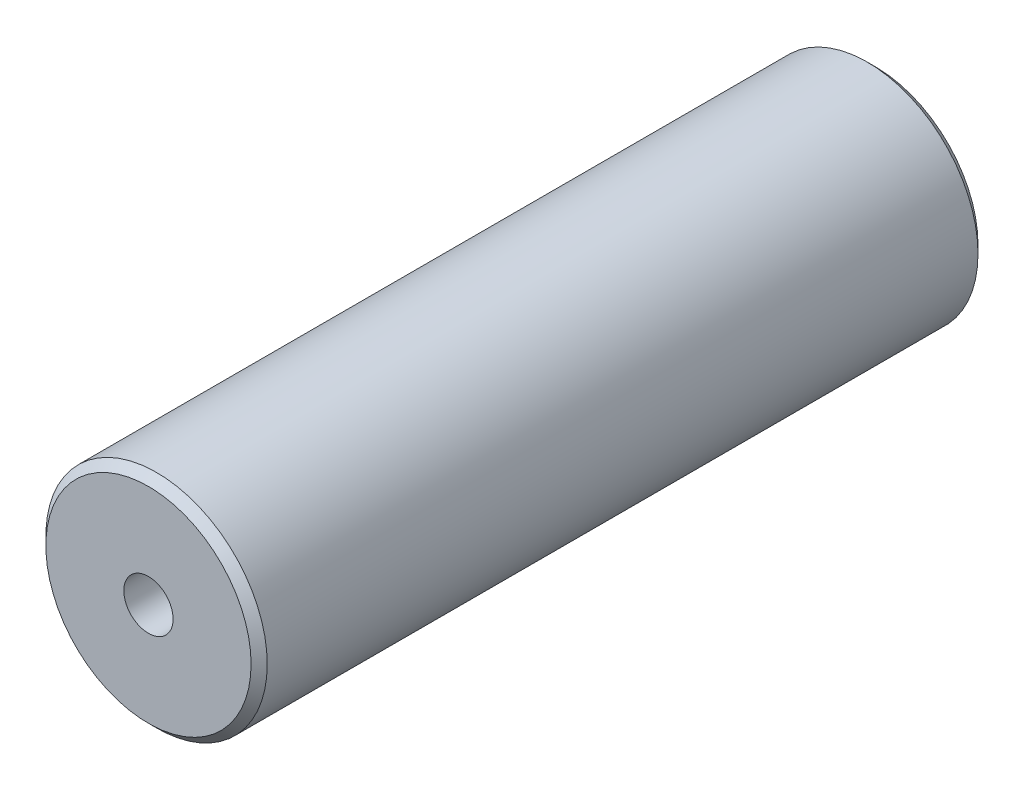
SolidWorks part; units mm, degrees
ref_plane "Front Plane" through (0, 0, 0) normal (0, 0, 1) x (1, 0, 0)
ref_plane "Top Plane" through (0, 0, 0) normal (0, 1, 0) x (1, 0, 0)
ref_plane "Right Plane" through (0, 0, 0) normal (1, 0, 0) x (0, 0, -1)
sketch "Sketch1" plane through (0, 0, 0) normal (0, 0, 1) x (1, 0, 0)
  circle A0 centre (0, 0) radius 13.7064
  circle A1 centre (0, 0) radius 3.05
  dimension "D1" = 6.1
extrude "Boss-Extrude1" add sketch "Sketch1" along normal blind 90
chamfer "Chamfer1" distance 1 angle 45 2 edges at (13.7064, 0, 90) (13.7064, 0, 0)
